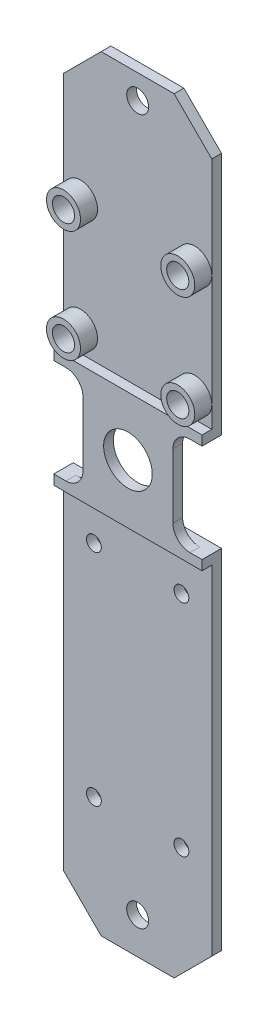
SolidWorks part; units mm, degrees
material "ABS"
ref_plane "正面" through (0, 0, 0) normal (1, 0, 0) x (0, 1, 0)
ref_plane "平面" through (0, 0, 0) normal (0, 0, 1) x (0, 1, 0)
ref_plane "右側面" through (0, 0, 0) normal (0, 1, 0) x (-1, 0, 0)
sketch "ｽｹｯﾁ1" plane through (0, 0, 0) normal (0, 0, 1) x (0, 1, 0)
  line L1 (0, 0) -> (157.5, 0)
  line L2 (0, 0) -> (0, 30.5)
  line L3 (0, 30.5) -> (157.5, 30.5)
  line L4 (157.5, 0) -> (157.5, 30.5)
  line L5 (0, 0) -> (157.5, 30.5) construction
  line L6 (0, 30.5) -> (157.5, 0) construction
  point P5 (78.75, 15.25)
  dimension "D1" = 157.5
  dimension "D2" = 30.5
extrude "ﾎﾞｽ - 押し出し1" add sketch "ｽｹｯﾁ1" along normal blind 2
sketch "ｽｹｯﾁ2" plane through (0, 0, 2) normal (0, 0, 1) x (1, 0, 0)
  line L1 (-24.25, 69.2) -> (-6.25, 69.2) construction
  line L2 (-24.25, 69.2) -> (-24.25, 24) construction
  line L3 (-24.25, 24) -> (-6.25, 24) construction
  line L4 (-6.25, 69.2) -> (-6.25, 24) construction
  line L5 (-24.25, 69.2) -> (-6.25, 24) construction
  line L6 (-24.25, 24) -> (-6.25, 69.2) construction
  line L7 (0, 157.5) -> (-30.5, 157.5) construction
  line L8 (-30.5, 0) -> (0, 0) construction
  point P11 (-15.25, 157.5)
  point P12 (-6.25, 69.2)
  point P13 (-24.25, 69.2)
  point P14 (-6.25, 24)
  point P15 (-24.25, 24)
  point P23 (-15.25, 46.6)
  dimension "D1" = 45.2
  dimension "D2" = 18
  dimension "D3" = 24
hole_wizard "Ø4.5 (3.05) 直径の穴1" positions "ｽｹｯﾁ2" profile "ｽｹｯﾁ3" hole size "Ø4.5" standard "JIS"
sketch "ｽｹｯﾁ3" plane through (-24.25, 24, 2) normal (1, 0, 0) x (0, -1, 0)
  line L0 (0, 0) -> (0, 2.5)
  line L1 (0, 2.5) -> (1.525, 2.5)
  line L2 (1.525, 2.5) -> (1.525, 0)
  line L5 (1.525, 0) -> (0, 0)
  line L10 (0, 2.5) -> (-1.525, 2.5) construction
  line L11 (0, -6.35) -> (0, 107.95) construction
  dimension "穴の直径" = 3.05
  dimension "穴の深さ" = 2.5
  dimension "ﾄﾞﾘﾙ角度" = 180
sketch "ｽｹｯﾁ4" plane through (0, 0, 2) normal (0, 0, 1) x (1, 0, 0)
  line L0 (0, 157.5) -> (-30.5, 157.5) construction
  line L1 (-27, 129) -> (-3.5, 129) construction
  line L2 (-27, 129) -> (-27, 106) construction
  line L3 (-27, 106) -> (-3.5, 106) construction
  line L4 (-3.5, 129) -> (-3.5, 106) construction
  line L5 (-27, 129) -> (-3.5, 106) construction
  line L6 (-27, 106) -> (-3.5, 129) construction
  circle A0 centre (-27, 129) radius 3.5
  circle A1 centre (-3.5, 129) radius 3.5
  circle A2 centre (-3.5, 106) radius 3.5
  circle A3 centre (-27, 106) radius 3.5
  point P4 (-15.25, 117.5)
  point P7 (-15.25, 157.5)
  point P9 (-27, 129)
  point P10 (-3.5, 129)
  point P11 (-3.5, 106)
  point P12 (-27, 106)
  dimension "D4" = 7
  dimension "D1" = 40
  dimension "D2" = 23.5
  dimension "D3" = 23
extrude "ﾎﾞｽ - 押し出し2" add sketch "ｽｹｯﾁ4" along normal blind 3.5
sketch "ｽｹｯﾁ5" plane through (0, 0, 5.5) normal (0, 0, 1) x (1, 0, 0)
  circle A0 centre (-27, 129) radius 2.275
  circle A1 centre (-3.5, 129) radius 2.275
  circle A2 centre (-3.5, 106) radius 2.275
  circle A3 centre (-27, 106) radius 2.275
  dimension "D1" = 4.55
extrude "ｶｯﾄ - 押し出し1" cut sketch "ｽｹｯﾁ5" against normal blind 3.5
sketch "ｽｹｯﾁ6" plane through (0, 0, 0) normal (0, 0, -1) x (1, 0, 0)
  line L0 (-30.5, -157.5) -> (-30.5, 0) construction
  line L1 (-30.5, -79.4) -> (0, -79.4)
  line L2 (-30.5, -79.4) -> (-30.5, -99.6)
  line L3 (-30.5, -99.6) -> (0, -99.6)
  line L4 (0, -79.4) -> (0, -99.6)
  line L5 (-30.5, -79.4) -> (0, -99.6) construction
  line L6 (-30.5, -99.6) -> (0, -79.4) construction
  line L7 (0, 0) -> (0, -157.5) construction
  line L8 (0, -157.5) -> (-30.5, -157.5) construction
  circle A0 centre (-27, -106) radius 3.5 construction
  circle A1 centre (-27, -106) radius 3.5 construction
  point P4 (-15.25, -89.5)
  dimension "D2" = 57.9
  dimension "D1" = 20.2
extrude "ｶｯﾄ - 押し出し3" cut sketch "ｽｹｯﾁ6" against normal blind 2.1
sketch "ｽｹｯﾁ9" plane through (0, 0, 2) normal (0, 0, 1) x (1, 0, 0)
  line L1 (-30.5, 79.4) -> (-30.5, 0) construction
  line L7 (-30.5, 77.4) -> (0, 77.4)
  line L8 (-30.5, 77.4) -> (-30.5, 101.6)
  line L15 (-30.5, 101.6) -> (0, 101.6)
  line L16 (0, 77.4) -> (0, 101.6)
  line L17 (-30.5, 77.4) -> (0, 101.6) construction
  line L21 (-30.5, 101.6) -> (0, 77.4) construction
  line L22 (0, 106) -> (0, 129) construction
  line L23 (0, 79.4) -> (-30.5, 79.4) construction
  line L24 (-30.5, 99.6) -> (0, 99.6) construction
  point P4 (-15.25, 89.5)
  dimension "D1" = 2
  dimension "D2" = 2
extrude "ﾎﾞｽ - 押し出し6" add sketch "ｽｹｯﾁ9" along normal blind 2
sketch "ｽｹｯﾁ12" plane through (0, 0, 5.5) normal (0, 0, 1) x (1, 0, 0)
  line L3 (-30.5, 77.4) -> (0, 77.4) construction
  line L4 (0, 77.4) -> (0, 101.6) construction
  circle A0 centre (-15.25, 89.5) radius 5
  point P2 (0, 0)
  point P4 (0, 0)
  point P7 (-15.25, 77.4)
  point P8 (-15.25, 88.3361)
  point P10 (0, 89.5)
  dimension "D2" = 10
extrude "ｶｯﾄ - 押し出し4" cut sketch "ｽｹｯﾁ12" against normal through all
sketch "ｽｹｯﾁ10" plane through (0, 0, 2) normal (0, 0, 1) x (1, 0, 0)
  line L0 (0, 157.5) -> (-30.5, 157.5) construction
  line L1 (-30.5, 0) -> (0, 0) construction
  point P0 (-15.25, 152.5)
  point P1 (-15.25, 7.5)
  point P4 (-15.25, 157.5)
  dimension "D1" = 5
  dimension "D2" = 7.5
hole_wizard "M4 すきま穴1" positions "ｽｹｯﾁ10" profile "ｽｹｯﾁ11" hole size "M4" standard "JIS" end condition through all
sketch "ｽｹｯﾁ11" plane through (-15.25, 152.5, 2) normal (1, 0, 0) x (0, -1, 0)
  line L0 (0, 0) -> (0, 2)
  line L1 (0, 2) -> (2.25, 2)
  line L2 (2.25, 2) -> (2.25, 0)
  line L5 (2.25, 0) -> (0, 0)
  line L11 (0, -6.35) -> (0, 107.95) construction
  dimension "通し穴の直径" = 4.5
  dimension "通し穴の深さ" = 2
sketch "ｽｹｯﾁ13" plane through (0, 0, 2) normal (0, 0, -1) x (1, 0, 0)
  line L0 (-30.5, -99.6) -> (0, -99.6) construction
  line L1 (0, -79.4) -> (-6, -79.4)
  line L2 (0, -79.4) -> (0, -99.6)
  line L3 (0, -99.6) -> (-6, -99.6)
  line L4 (-6, -79.4) -> (-6, -99.6)
  line L5 (0, -79.4) -> (-6, -99.6) construction
  line L6 (0, -99.6) -> (-6, -79.4) construction
  line L7 (-15.25, -79.4) -> (-15.25, -99.6) construction
  line L8 (0, -79.4) -> (-30.5, -79.4) construction
  line L9 (-30.5, -99.6) -> (-24.5, -99.6)
  line L10 (-24.5, -79.4) -> (-24.5, -99.6)
  line L11 (-30.5, -79.4) -> (-24.5, -79.4)
  line L12 (-30.5, -79.4) -> (-30.5, -99.6)
  point P4 (-3, -89.5)
  dimension "D1" = 6
extrude "ｶｯﾄ - 押し出し5" cut sketch "ｽｹｯﾁ13" against normal through all
fillet "ﾌｨﾚｯﾄ8" radius 3.5 4 edges at (-6, 79.4, 3) (-6, 99.6, 3) (-24.5, 99.6, 3) (-24.5, 79.4, 3)
chamfer "面取り1" distance 7.75 angle 45 4 edges at (0, 157.5, 1) (-30.5, 157.5, 1) (-30.5, 0, 1) (0, 0, 1)
